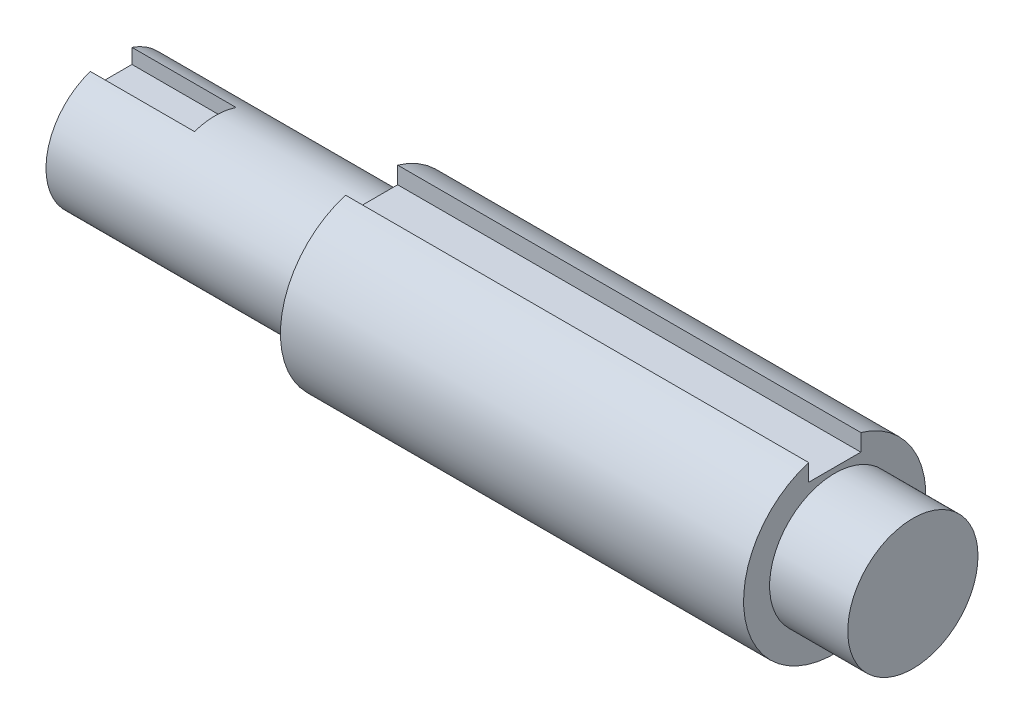
SolidWorks part; units mm, degrees
ref_plane "Front Plane" through (0, 0, 0) normal (0, 0, 1) x (1, 0, 0)
ref_plane "Top Plane" through (0, 0, 0) normal (0, 1, 0) x (1, 0, 0)
ref_plane "Right Plane" through (0, 0, 0) normal (1, 0, 0) x (0, 0, -1)
sketch "Sketch1" plane through (0, 0, 0) normal (1, 0, 0) x (0, 0, -1)
  line L1 (4, 16) -> (-4, 16)
  line L2 (4, 16) -> (4, 9)
  line L3 (4, 9) -> (-4, 9)
  line L4 (-4, 16) -> (-4, 9)
  line L5 (4, 16) -> (-4, 9) construction
  line L6 (4, 9) -> (-4, 16) construction
  circle A0 centre (0, 0) radius 12.5
  point P3 (0, 12.5)
  dimension "D1" = 25
  dimension "D2" = 7
  dimension "D3" = 8
extrude "Boss-Extrude1" add sketch "Sketch1" along normal blind 20 contours L4 A0 L2 L3
sketch "Sketch2" plane through (20, 0, 0) normal (1, 0, 0) x (0, 0, -1)
  circle A0 centre (0, 0) radius 12.5
  dimension "D1" = 25
extrude "Boss-Extrude2" add sketch "Sketch2" along normal blind 10
sketch "Sketch3" plane through (30, 0, 0) normal (1, 0, 0) x (0, 0, -1)
  circle A0 centre (0, 0) radius 12.5
  dimension "D1" = 25
extrude "Boss-Extrude3" add sketch "Sketch3" along normal blind 20
sketch "Sketch4" plane through (50, 0, 0) normal (1, 0, 0) x (0, 0, -1)
  line L1 (5, 21.5) -> (-5, 21.5)
  line L2 (5, 21.5) -> (5, 13.5)
  line L3 (5, 13.5) -> (-5, 13.5)
  line L4 (-5, 21.5) -> (-5, 13.5)
  line L5 (5, 21.5) -> (-5, 13.5) construction
  line L6 (5, 13.5) -> (-5, 21.5) construction
  circle A0 centre (0, 0) radius 17.5
  point P3 (0, 17.5)
  circle M2 centre (0, 0) radius 12.5
  dimension "D1" = 35
  dimension "D2" = 8
  dimension "D3" = 10
extrude "Boss-Extrude6" add sketch "Sketch4" along normal blind 88.9 contours M2 | L4 A0 L2 L3 M2
sketch "Sketch6" plane through (138.9, 0, 0) normal (1, 0, 0) x (0, 0, -1)
  circle A0 centre (0, 0) radius 12.5
  dimension "D1" = 25
extrude "Boss-Extrude7" add sketch "Sketch6" along normal blind 15
